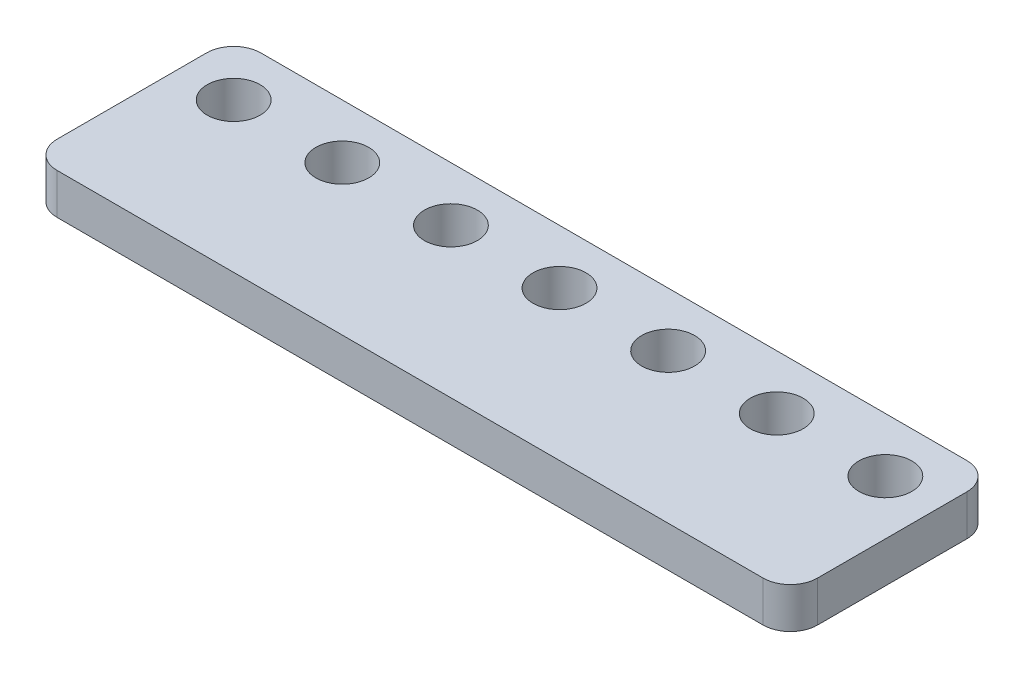
SolidWorks part; units mm, degrees
ref_plane "Front Plane" through (0, 0, 0) normal (0, 0, 1) x (1, 0, 0)
ref_plane "Top Plane" through (0, 0, 0) normal (0, 1, 0) x (1, 0, 0)
ref_plane "Right Plane" through (0, 0, 0) normal (1, 0, 0) x (0, 0, -1)
sketch "Sketch1" plane through (0, 0, 0) normal (0, 1, 0) x (1, 0, 0)
  line L1 (-54, 0) -> (-2, 0)
  line L2 (-56, -2) -> (-56, -13)
  line L3 (-54, -15) -> (-2, -15)
  line L4 (0, -2) -> (0, -13)
  arc A0 (-2, -15) -> (0, -13) centre (-2, -13) ccw
  arc A1 (-56, -13) -> (-54, -15) centre (-54, -13) ccw
  arc A2 (-54, 0) -> (-56, -2) centre (-54, -2) ccw
  arc A3 (-2, 0) -> (0, -2) centre (-2, -2) cw
  point P7 (0, -15)
  point P12 (-56, 0)
  point P15 (0, 0)
  dimension "D3" = 2
  dimension "D1" = 56
  dimension "D2" = 15
extrude "Boss-Extrude1" add sketch "Sketch1" along normal blind 3
sketch "Sketch2" plane through (0, 3, 0) normal (0, 1, 0) x (1, 0, 0)
  line L1 (0, -13) -> (0, -2) construction
  line L2 (-4, -4) -> (-56, -4) construction
  line L3 (-56, -2) -> (-56, -13) construction
  line L4 (-2, 0) -> (-54, 0) construction
  circle A0 centre (-4, -4) radius 1.95
  circle A1 centre (-12, -4) radius 1.95
  circle A2 centre (-76, -4) radius 1.95
  circle A3 centre (-68, -4) radius 1.95
  circle A4 centre (-60, -4) radius 1.95
  circle A5 centre (-52, -4) radius 1.95
  circle A6 centre (-44, -4) radius 1.95
  circle A7 centre (-36, -4) radius 1.95
  circle A8 centre (-28, -4) radius 1.95
  circle A9 centre (-20, -4) radius 1.95
  dimension "D1" = 3.9
  dimension "D4" = 3.9
  dimension "D7" = 3.9
  dimension "D8" = 3.9
  dimension "D9" = 3.9
  dimension "D10" = 3.9
  dimension "D11" = 3.9
  dimension "D12" = 3.9
  dimension "D13" = 3.9
  dimension "D14" = 3.9
  dimension "D3" = 4
  dimension "D5" = 8
  dimension "D15" = 8
  dimension "D16" = 8
  dimension "D17" = 8
  dimension "D18" = 8
  dimension "D19" = 8
  dimension "D20" = 8
  dimension "D21" = 8
  dimension "D22" = 4
extrude "Cut-Extrude1" cut sketch "Sketch2" against normal through all
